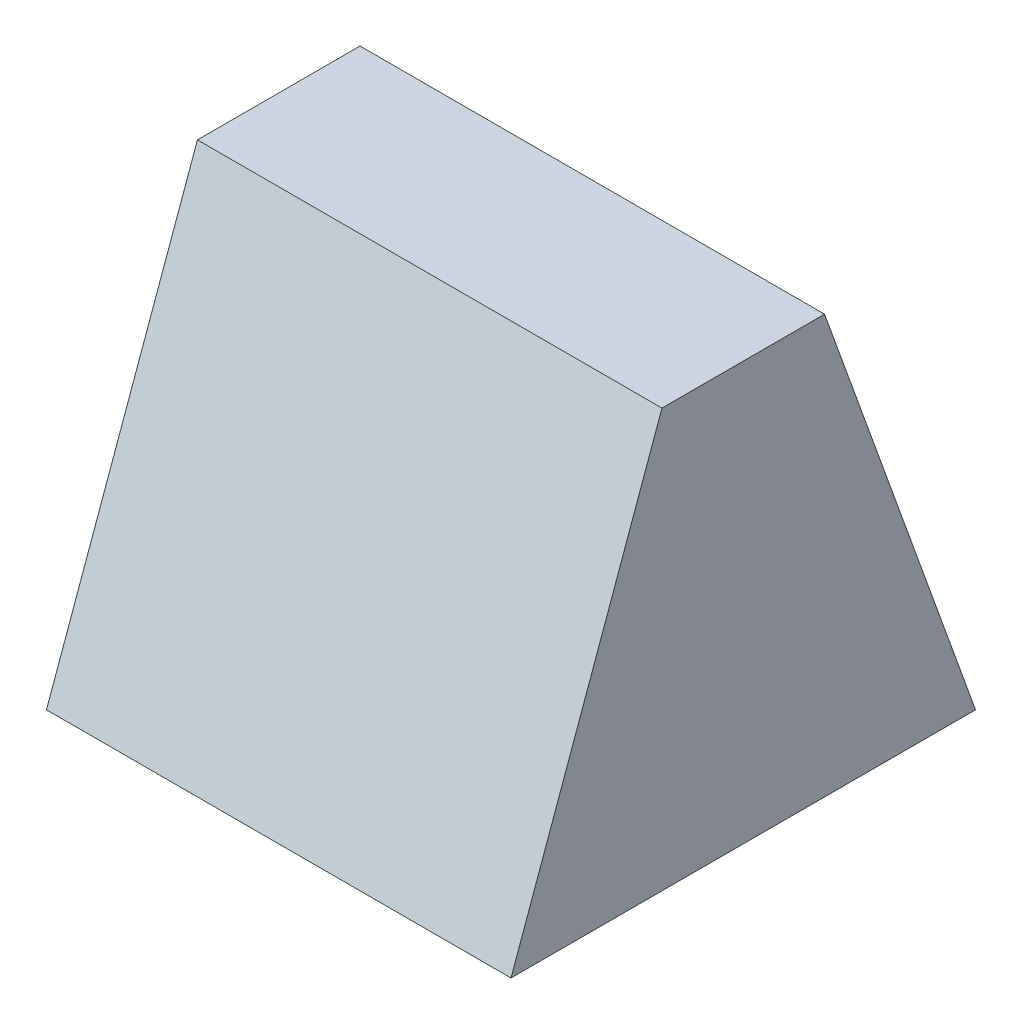
SolidWorks part; units mm, degrees
ref_plane "Front Plane" through (0, 0, 0) normal (0, 0, 1) x (1, 0, 0)
ref_plane "Top Plane" through (0, 0, 0) normal (0, 1, 0) x (1, 0, 0)
ref_plane "Right Plane" through (0, 0, 0) normal (1, 0, 0) x (0, 0, -1)
sketch "Schizzo1" plane through (0, -56.3363, -180.9473) normal (-1, 0, 0) x (0, 0, 1)
  line L0 (5, 13.4104) -> (-5, 13.4104)
  line L1 (-5, 13.4104) -> (-1.75, 22.4104)
  line L2 (-1.75, 22.4104) -> (1.75, 22.4104)
  line L3 (1.75, 22.4104) -> (5, 13.4104)
  line L4 (1.75, 22.4104) -> (1.75, 13.4104) construction
  line L5 (-1.75, 22.4104) -> (-1.75, 13.4104) construction
  line L6 (1.75, 22.4104) -> (0, 27.2566) construction
  line L7 (0, 27.2566) -> (-1.75, 22.4104) construction
  dimension "D1" = 10
  dimension "D2" = 3.5
  dimension "D3" = 9
  dimension "D6" = 3.25
  dimension "D7" = 3.25
  dimension "D8" = 39.71
extrude "Estrusione-Estrusione1" add sketch "Schizzo1" along normal blind 10
